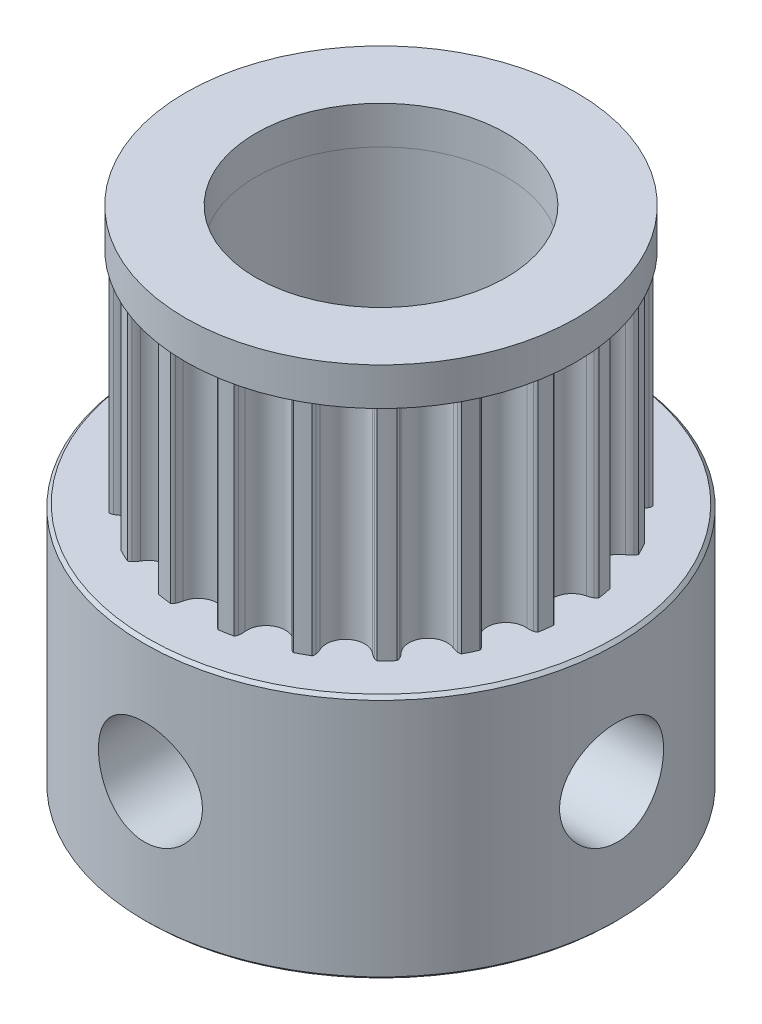
SolidWorks part; units mm, degrees
material "6061 slitina"
ref_plane "Přední rovina" through (0, 0, 0) normal (0, 0, 1) x (1, 0, 0)
ref_plane "Horní rovina" through (0, 0, 0) normal (0, 1, 0) x (1, 0, 0)
ref_plane "Pravá rovina" through (0, 0, 0) normal (1, 0, 0) x (0, 0, -1)
sketch "Skica1" plane through (0, 0, 0) normal (0, 1, 0) x (1, 0, 0)
  circle A0 centre (0, 0) radius 2.5
  arc B0 (-5.7301, 1.0983) -> (-5.3872, 2.2403) centre (-5.6803, 1.7058) ccw
  arc B1 (-5.7301, 1.0983) -> (-5.922, 1.0859) centre (-5.7841, 0.4401) ccw
  arc B2 (-5.922, 1.0859) -> (-6.0197, 1.0387) centre (-5.8743, 0.8624) ccw
  arc B3 (-6.0197, 1.0387) -> (-6.0791, 0.6004) centre (0, 0) ccw
  arc B4 (-6.0791, 0.6004) -> (-5.9974, 0.5289) centre (-5.892, 0.7317) ccw
  arc B5 (-5.9974, 0.5289) -> (-5.8158, 0.466) centre (-5.6927, 1.1148) ccw
  arc B6 (-5.7891, -0.7262) -> (-5.8158, 0.466) centre (-5.9294, -0.133) ccw
  arc B7 (-5.7891, -0.7262) -> (-5.9677, -0.7972) centre (-5.637, -1.3689) ccw
  arc B8 (-5.9677, -0.7972) -> (-6.0461, -0.8723) centre (-5.8532, -0.9951) ccw
  arc B9 (-6.0461, -0.8723) -> (-5.9671, -1.3075) centre (0, 0) ccw
  arc B10 (-5.9671, -1.3075) -> (-5.8673, -1.3503) centre (-5.8297, -1.1248) ccw
  arc B11 (-5.8673, -1.3503) -> (-5.6751, -1.354) centre (-5.7586, -0.6989) ccw
  arc B12 (-5.2813, -2.4796) -> (-5.6751, -1.354) centre (-5.5981, -1.9587) ccw
  arc B13 (-5.2813, -2.4796) -> (-5.4293, -2.6023) centre (-4.9381, -3.0438) ccw
  arc B14 (-5.4293, -2.6023) -> (-5.4806, -2.698) centre (-5.2593, -2.7551) ccw
  arc B15 (-5.4806, -2.698) -> (-5.271, -3.0875) centre (0, 0) ccw
  arc B16 (-5.271, -3.0875) -> (-5.1629, -3.0973) centre (-5.1968, -2.8713) ccw
  arc B17 (-5.1629, -3.0973) -> (-4.979, -3.0415) centre (-5.2608, -2.4442) ccw
  arc B18 (-4.2566, -3.9902) -> (-4.979, -3.0415) centre (-4.7188, -3.5928) ccw
  arc B19 (-4.2566, -3.9902) -> (-4.3594, -4.1527) centre (-3.7559, -4.4208) ccw
  arc B20 (-4.3594, -4.1527) -> (-4.3786, -4.2595) centre (-4.1505, -4.2455) ccw
  arc B21 (-4.3786, -4.2595) -> (-4.059, -4.5652) centre (0, 0) ccw
  arc B22 (-4.059, -4.5652) -> (-3.9531, -4.5412) centre (-4.0552, -4.3366) ccw
  arc B23 (-3.9531, -4.5412) -> (-3.7954, -4.4312) centre (-4.248, -3.9503) ccw
  arc B24 (-2.8152, -5.1103) -> (-3.7954, -4.4312) centre (-3.3776, -4.8751) ccw
  arc B25 (-2.8152, -5.1103) -> (-2.8628, -5.2965) centre (-2.2059, -5.3651) ccw
  arc B26 (-2.8628, -5.2965) -> (-2.8481, -5.4041) centre (-2.6354, -5.3203) ccw
  arc B27 (-2.8481, -5.4041) -> (-2.4496, -5.596) centre (0, 0) ccw
  arc B28 (-2.4496, -5.596) -> (-2.3563, -5.5405) centre (-2.5166, -5.3775) ccw
  arc B29 (-2.3563, -5.5405) -> (-2.2403, -5.3872) centre (-2.8194, -5.0696) ccw
  arc B30 (-1.0983, -5.7301) -> (-2.2403, -5.3872) centre (-1.7058, -5.6803) ccw
  arc B31 (-1.0983, -5.7301) -> (-1.0859, -5.922) centre (-0.4401, -5.7841) ccw
  arc B32 (-1.0859, -5.922) -> (-1.0387, -6.0197) centre (-0.8624, -5.8743) ccw
  arc B33 (-1.0387, -6.0197) -> (-0.6004, -6.0791) centre (0, 0) ccw
  arc B34 (-0.6004, -6.0791) -> (-0.5289, -5.9974) centre (-0.7317, -5.892) ccw
  arc B35 (-0.5289, -5.9974) -> (-0.466, -5.8158) centre (-1.1148, -5.6927) ccw
  arc B36 (0.7262, -5.7891) -> (-0.466, -5.8158) centre (0.133, -5.9294) ccw
  arc B37 (0.7262, -5.7891) -> (0.7972, -5.9677) centre (1.3689, -5.637) ccw
  arc B38 (0.7972, -5.9677) -> (0.8723, -6.0461) centre (0.9951, -5.8532) ccw
  arc B39 (0.8723, -6.0461) -> (1.3075, -5.9671) centre (0, 0) ccw
  arc B40 (1.3075, -5.9671) -> (1.3503, -5.8673) centre (1.1248, -5.8297) ccw
  arc B41 (1.3503, -5.8673) -> (1.354, -5.6751) centre (0.6989, -5.7586) ccw
  arc B42 (2.4796, -5.2813) -> (1.354, -5.6751) centre (1.9587, -5.5981) ccw
  arc B43 (2.4796, -5.2813) -> (2.6023, -5.4293) centre (3.0438, -4.9381) ccw
  arc B44 (2.6023, -5.4293) -> (2.698, -5.4806) centre (2.7551, -5.2593) ccw
  arc B45 (2.698, -5.4806) -> (3.0875, -5.271) centre (0, 0) ccw
  arc B46 (3.0875, -5.271) -> (3.0973, -5.1629) centre (2.8713, -5.1968) ccw
  arc B47 (3.0973, -5.1629) -> (3.0415, -4.979) centre (2.4442, -5.2608) ccw
  arc B48 (3.9902, -4.2566) -> (3.0415, -4.979) centre (3.5928, -4.7188) ccw
  arc B49 (3.9902, -4.2566) -> (4.1527, -4.3594) centre (4.4208, -3.7559) ccw
  arc B50 (4.1527, -4.3594) -> (4.2595, -4.3786) centre (4.2455, -4.1505) ccw
  arc B51 (4.2595, -4.3786) -> (4.5652, -4.059) centre (0, 0) ccw
  arc B52 (4.5652, -4.059) -> (4.5412, -3.9531) centre (4.3366, -4.0552) ccw
  arc B53 (4.5412, -3.9531) -> (4.4312, -3.7954) centre (3.9503, -4.248) ccw
  arc B54 (5.1103, -2.8152) -> (4.4312, -3.7954) centre (4.8751, -3.3776) ccw
  arc B55 (5.1103, -2.8152) -> (5.2965, -2.8628) centre (5.3651, -2.2059) ccw
  arc B56 (5.2965, -2.8628) -> (5.4041, -2.8481) centre (5.3203, -2.6354) ccw
  arc B57 (5.4041, -2.8481) -> (5.596, -2.4496) centre (0, 0) ccw
  arc B58 (5.596, -2.4496) -> (5.5405, -2.3563) centre (5.3775, -2.5166) ccw
  arc B59 (5.5405, -2.3563) -> (5.3872, -2.2403) centre (5.0696, -2.8194) ccw
  arc B60 (5.7301, -1.0983) -> (5.3872, -2.2403) centre (5.6803, -1.7058) ccw
  arc B61 (5.7301, -1.0983) -> (5.922, -1.0859) centre (5.7841, -0.4401) ccw
  arc B62 (5.922, -1.0859) -> (6.0197, -1.0387) centre (5.8743, -0.8624) ccw
  arc B63 (6.0197, -1.0387) -> (6.0791, -0.6004) centre (0, 0) ccw
  arc B64 (6.0791, -0.6004) -> (5.9974, -0.5289) centre (5.892, -0.7317) ccw
  arc B65 (5.9974, -0.5289) -> (5.8158, -0.466) centre (5.6927, -1.1148) ccw
  arc B66 (5.7891, 0.7262) -> (5.8158, -0.466) centre (5.9294, 0.133) ccw
  arc B67 (5.7891, 0.7262) -> (5.9677, 0.7972) centre (5.637, 1.3689) ccw
  arc B68 (5.9677, 0.7972) -> (6.0461, 0.8723) centre (5.8532, 0.9951) ccw
  arc B69 (6.0461, 0.8723) -> (5.9671, 1.3075) centre (0, 0) ccw
  arc B70 (5.9671, 1.3075) -> (5.8673, 1.3503) centre (5.8297, 1.1248) ccw
  arc B71 (5.8673, 1.3503) -> (5.6751, 1.354) centre (5.7586, 0.6989) ccw
  arc B72 (5.2813, 2.4796) -> (5.6751, 1.354) centre (5.5981, 1.9587) ccw
  arc B73 (5.2813, 2.4796) -> (5.4293, 2.6023) centre (4.9381, 3.0438) ccw
  arc B74 (5.4293, 2.6023) -> (5.4806, 2.698) centre (5.2593, 2.7551) ccw
  arc B75 (5.4806, 2.698) -> (5.271, 3.0875) centre (0, 0) ccw
  arc B76 (5.271, 3.0875) -> (5.1629, 3.0973) centre (5.1968, 2.8713) ccw
  arc B77 (5.1629, 3.0973) -> (4.979, 3.0415) centre (5.2608, 2.4442) ccw
  arc B78 (4.2566, 3.9902) -> (4.979, 3.0415) centre (4.7188, 3.5928) ccw
  arc B79 (4.2566, 3.9902) -> (4.3594, 4.1527) centre (3.7559, 4.4208) ccw
  arc B80 (4.3594, 4.1527) -> (4.3786, 4.2595) centre (4.1505, 4.2455) ccw
  arc B81 (4.3786, 4.2595) -> (4.059, 4.5652) centre (0, 0) ccw
  arc B82 (4.059, 4.5652) -> (3.9531, 4.5412) centre (4.0552, 4.3366) ccw
  arc B83 (3.9531, 4.5412) -> (3.7954, 4.4312) centre (4.248, 3.9503) ccw
  arc B84 (2.8152, 5.1103) -> (3.7954, 4.4312) centre (3.3776, 4.8751) ccw
  arc B85 (2.8152, 5.1103) -> (2.8628, 5.2965) centre (2.2059, 5.3651) ccw
  arc B86 (2.8628, 5.2965) -> (2.8481, 5.4041) centre (2.6354, 5.3203) ccw
  arc B87 (2.8481, 5.4041) -> (2.4496, 5.596) centre (0, 0) ccw
  arc B88 (2.4496, 5.596) -> (2.3563, 5.5405) centre (2.5166, 5.3775) ccw
  arc B89 (2.3563, 5.5405) -> (2.2403, 5.3872) centre (2.8194, 5.0696) ccw
  arc B90 (1.0983, 5.7301) -> (2.2403, 5.3872) centre (1.7058, 5.6803) ccw
  arc B91 (1.0983, 5.7301) -> (1.0859, 5.922) centre (0.4401, 5.7841) ccw
  arc B92 (1.0859, 5.922) -> (1.0387, 6.0197) centre (0.8624, 5.8743) ccw
  arc B93 (1.0387, 6.0197) -> (0.6004, 6.0791) centre (0, 0) ccw
  arc B94 (0.6004, 6.0791) -> (0.5289, 5.9974) centre (0.7317, 5.892) ccw
  arc B95 (0.5289, 5.9974) -> (0.466, 5.8158) centre (1.1148, 5.6927) ccw
  arc B96 (-0.7262, 5.7891) -> (0.466, 5.8158) centre (-0.133, 5.9294) ccw
  arc B97 (-0.7262, 5.7891) -> (-0.7972, 5.9677) centre (-1.3689, 5.637) ccw
  arc B98 (-0.7972, 5.9677) -> (-0.8723, 6.0461) centre (-0.9951, 5.8532) ccw
  arc B99 (-0.8723, 6.0461) -> (-1.3075, 5.9671) centre (0, 0) ccw
  arc B100 (-1.3075, 5.9671) -> (-1.3503, 5.8673) centre (-1.1248, 5.8297) ccw
  arc B101 (-1.3503, 5.8673) -> (-1.354, 5.6751) centre (-0.6989, 5.7586) ccw
  arc B102 (-2.4796, 5.2813) -> (-1.354, 5.6751) centre (-1.9587, 5.5981) ccw
  arc B103 (-2.4796, 5.2813) -> (-2.6023, 5.4293) centre (-3.0438, 4.9381) ccw
  arc B104 (-2.6023, 5.4293) -> (-2.698, 5.4806) centre (-2.7551, 5.2593) ccw
  arc B105 (-2.698, 5.4806) -> (-3.0875, 5.271) centre (0, 0) ccw
  arc B106 (-3.0875, 5.271) -> (-3.0973, 5.1629) centre (-2.8713, 5.1968) ccw
  arc B107 (-3.0973, 5.1629) -> (-3.0415, 4.979) centre (-2.4442, 5.2608) ccw
  arc B108 (-3.9902, 4.2566) -> (-3.0415, 4.979) centre (-3.5928, 4.7188) ccw
  arc B109 (-3.9902, 4.2566) -> (-4.1527, 4.3594) centre (-4.4208, 3.7559) ccw
  arc B110 (-4.1527, 4.3594) -> (-4.2595, 4.3786) centre (-4.2455, 4.1505) ccw
  arc B111 (-4.2595, 4.3786) -> (-4.5652, 4.059) centre (0, 0) ccw
  arc B112 (-4.5652, 4.059) -> (-4.5412, 3.9531) centre (-4.3366, 4.0552) ccw
  arc B113 (-4.5412, 3.9531) -> (-4.4312, 3.7954) centre (-3.9503, 4.248) ccw
  arc B114 (-5.1103, 2.8152) -> (-4.4312, 3.7954) centre (-4.8751, 3.3776) ccw
  arc B115 (-5.1103, 2.8152) -> (-5.2965, 2.8628) centre (-5.3651, 2.2059) ccw
  arc B116 (-5.2965, 2.8628) -> (-5.4041, 2.8481) centre (-5.3203, 2.6354) ccw
  arc B117 (-5.4041, 2.8481) -> (-5.596, 2.4496) centre (0, 0) ccw
  arc B118 (-5.596, 2.4496) -> (-5.5405, 2.3563) centre (-5.3775, 2.5166) ccw
  arc B119 (-5.5405, 2.3563) -> (-5.3872, 2.2403) centre (-5.0696, 2.8194) ccw
  dimension "D1" = 5
sketch_block_instance "Blok1-1"
sketch_block "Blok1"
extrude "Přidat vysunutím1" add sketch "Skica1" along normal blind 7 from offset 7.8
sketch "Skica2" plane through (0, 7.8, 0) normal (0, -1, 0) x (1, 0, 0)
  circle A0 centre (0, 0) radius 3.5
  circle A1 centre (0, 0) radius 2.5 construction
  circle A2 centre (0, 0) radius 2.5
  dimension "D1" = 7
extrude "Přidat vysunutím2" add sketch "Skica2" along normal blind 7.8
sketch "Skica3" plane through (0, 14.8, 0) normal (0, 1, 0) x (1, 0, 0)
  circle A0 centre (0, 0) radius 3.5
  circle A1 centre (0, 0) radius 2.5 construction
  circle A2 centre (0, 0) radius 2.5
  dimension "D1" = 7
extrude "Přidat vysunutím3" add sketch "Skica3" along normal blind 1.2
sketch "Skica5" plane through (0, 16, 0) normal (0, 1, 0) x (1, 0, 0)
  circle A0 centre (0, 0) radius 7.5
  circle A3 centre (0, 0) radius 3.5 construction
  circle A4 centre (0, 0) radius 3.5
  dimension "D1" = 15
extrude "Přidat vysunutím4" add sketch "Skica5" against normal up to surface (1.2 mm away) separate body up to face at (0, 14.8, 0)
sketch "Skica6" plane through (0, 0, 0) normal (0, -1, 0) x (1, 0, 0)
  circle A0 centre (0, 0) radius 7.5
  circle A1 centre (0, 0) radius 3.5 construction
  circle A2 centre (0, 0) radius 3.5
  circle A3 centre (0, 0) radius 7.5 construction
extrude "Přidat vysunutím5" add sketch "Skica6" against normal up to surface (7.8 mm away) separate body up to face at (0, 7.8, 0)
hole_wizard "M4 závit1" positions "3DSkica2" profile "Skica8" tap size "M4" standard "ISO"
sketch3d "3DSkica2"
  line L0 (0, 0, 7.5) -> (0, 3.9, 7.5) construction
  line L1 (7.5, 0, 0) -> (7.5, 3.9, 0) construction
  circle A0 centre (0, 0, 0) radius 7.5 construction
  point P0 (0, 3.9, 7.5)
  point P2 (7.5, 3.9, 0)
  point P34 (0, -7.5, 0)
  dimension "D1" = 3.9
sketch "Skica8" plane through (0, 3.9, 7.5) normal (1, 0, 0) x (0, -1, 0)
  line L0 (0, 0) -> (0, 11)
  line L1 (0, 11) -> (1.65, 11)
  line L2 (1.65, 11) -> (1.65, 0)
  line L5 (1.65, 0) -> (0, 0)
  line L11 (0, -6.35) -> (0, 107.95) construction
  dimension "Průměr závitníku" = 3.3
  dimension "Hloubka závitníku" = 11
cosmetic thread "Závit díry1" parameters "D2"=4
cosmetic thread "Závit díry2" parameters "D2"=4
chamfer "Zkosení1" distance 0.1 angle 45 2 edges at (0, 14.8, 7.5) (0, 16, 7.5)
chamfer "Zkosení2" distance 0.1 angle 45 2 edges at (0, 0, -2.5) (0, 16, 2.5)
chamfer "Zkosení3" distance 0.1 angle 45 2 edges at (0, 0, -7.5) (0, 7.8, 7.5)
sketch "Sketch2" plane through (0, 0, 0) normal (0, -1, 0) x (1, 0, 0)
  circle A0 centre (0, 0) radius 3.97
extrude "Cut-Extrude1" cut sketch "Sketch2" against normal blind 20 contours A0
sketch "Sketch4" plane through (0, 16, 0) normal (0, 1, 0) x (1, 0, 0)
  circle A0 centre (0, 0) radius 6.2
extrude "Cut-Extrude6" cut sketch "Sketch4" against normal blind 5 flip side to cut
